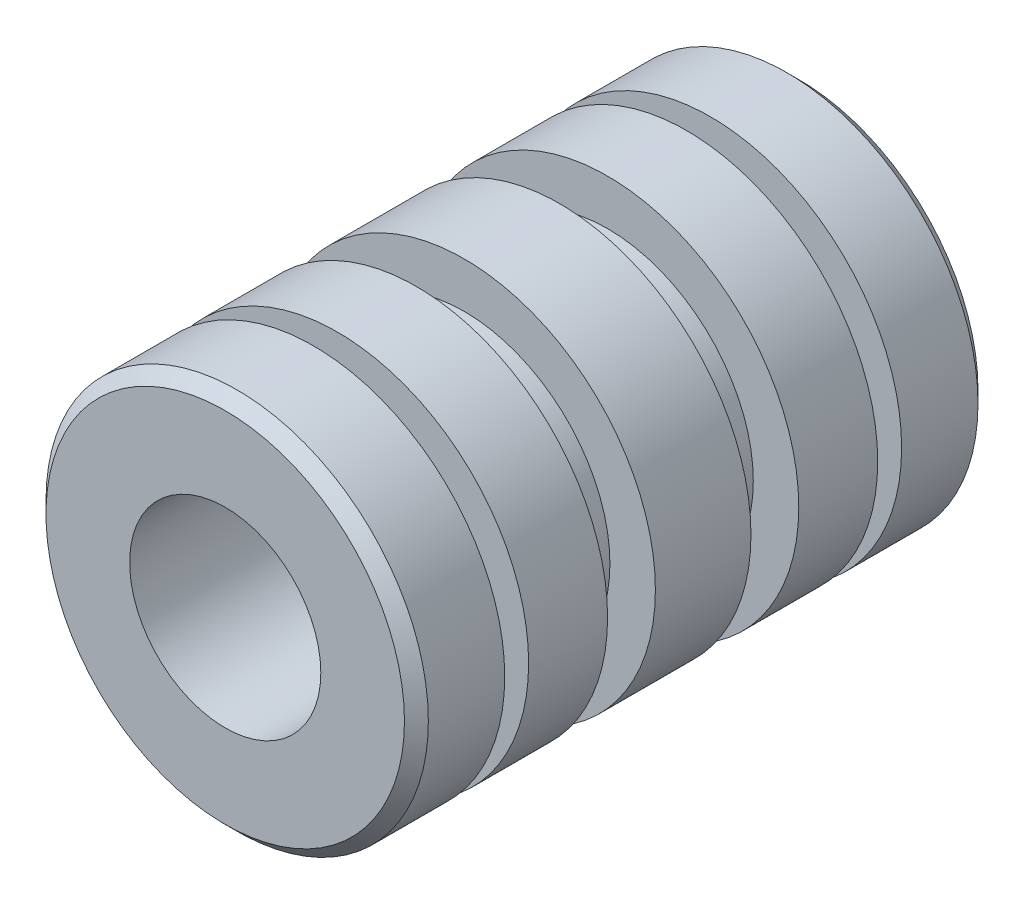
SolidWorks part; units mm, degrees
ref_plane "Front Plane" through (0, 0, 0) normal (0, 0, 1) x (1, 0, 0)
ref_plane "Top Plane" through (0, 0, 0) normal (0, 1, 0) x (1, 0, 0)
ref_plane "Right Plane" through (0, 0, 0) normal (1, 0, 0) x (0, 0, -1)
sketch "Sketch2" plane through (0, 0, 0) normal (0, 0, 1) x (1, 0, 0)
  circle A0 centre (0, 0) radius 6.35
  dimension "D1" = 12.7
extrude "Boss-Extrude1" add sketch "Sketch2" along normal blind 19.05
sketch "Sketch3" plane through (0, 0, 19.05) normal (0, 0, 1) x (1, 0, 0)
  circle A0 centre (0, 0) radius 3.175
  dimension "D1" = 6.35
extrude "Cut-Extrude1" cut sketch "Sketch3" against normal through all
sketch "Sketch4" plane through (0, 0, 0) normal (0, 1, 0) x (1, 0, 0)
  line L0 (6.3084, 0) -> (6.35, -19.05) construction
  line L1 (0, -19.05) -> (0, 0) construction
  line L2 (7.9167, -3.7274) -> (4.7417, -15.3225) construction
  line L3 (7.9167, -15.3225) -> (4.7417, -15.3225)
  line L4 (7.9167, -15.3225) -> (7.9167, -16.1163)
  line L5 (7.9167, -16.1163) -> (4.7417, -16.1163)
  line L6 (4.7417, -15.3225) -> (4.7417, -16.1163)
  line L7 (7.9167, -15.3225) -> (4.7417, -16.1163) construction
  line L8 (7.9167, -16.1163) -> (4.7417, -15.3225) construction
  line L10 (4.7417, -2.9337) -> (7.9167, -2.9337)
  line L11 (4.7417, -2.9337) -> (4.7417, -3.7274)
  line L12 (4.7417, -3.7274) -> (7.9167, -3.7274)
  line L13 (7.9167, -2.9337) -> (7.9167, -3.7274)
  line L14 (4.7417, -2.9337) -> (7.9167, -3.7274) construction
  line L15 (4.7417, -3.7274) -> (7.9167, -2.9337) construction
  point P8 (6.3292, -9.525)
  dimension "D1" = 13.1826
  dimension "D2" = 0.125
  dimension "D3" = 0.7938
  dimension "D4" = 19.05
revolve "Cut-Revolve1" cut sketch "Sketch4" angle 360 about axis through (0, 0, 19.05) along (0, 0, -1)
sketch "Sketch5" plane through (0, 0, 0) normal (0, 1, 0) x (1, 0, 0)
  line L0 (6.35, -15.3226) -> (6.35, -3.7275) construction
  line L1 (4.8398, -11.1125) -> (7.8602, -11.1125)
  line L2 (4.8398, -11.1125) -> (4.8398, -12.7)
  line L3 (4.8398, -12.7) -> (7.8602, -12.7)
  line L4 (7.8602, -11.1125) -> (7.8602, -12.7)
  line L5 (4.8398, -11.1125) -> (7.8602, -12.7) construction
  line L6 (4.8398, -12.7) -> (7.8602, -11.1125) construction
  line L7 (7.8602, -12.7) -> (4.8398, -6.35) construction
  line L8 (4.8398, -7.9375) -> (7.8602, -7.9375)
  line L9 (4.8398, -7.9375) -> (4.8398, -6.35)
  line L10 (4.8398, -6.35) -> (7.8602, -6.35)
  line L11 (7.8602, -7.9375) -> (7.8602, -6.35)
  line L12 (4.8398, -7.9375) -> (7.8602, -6.35) construction
  line L13 (4.8398, -6.35) -> (7.8602, -7.9375) construction
  line L14 (6.35, 0) -> (6.35, -19.05) construction
  line L15 (-6.35, -19.05) -> (6.35, -19.05) construction
  point P0 (6.35, -11.9062)
  point P7 (6.35, -7.1437)
  point P18 (6.35, -9.525)
  dimension "D1" = 6.35
  dimension "D2" = 1.5875
chamfer "Chamfer1" distance 0.3969 angle 45 2 edges at (6.35, 0, 0) (6.35, 0, 19.05)
revolve "Cut-Revolve2" cut sketch "Sketch5" angle 360 about axis through (0, 0, 19.05) along (0, 0, -1)
